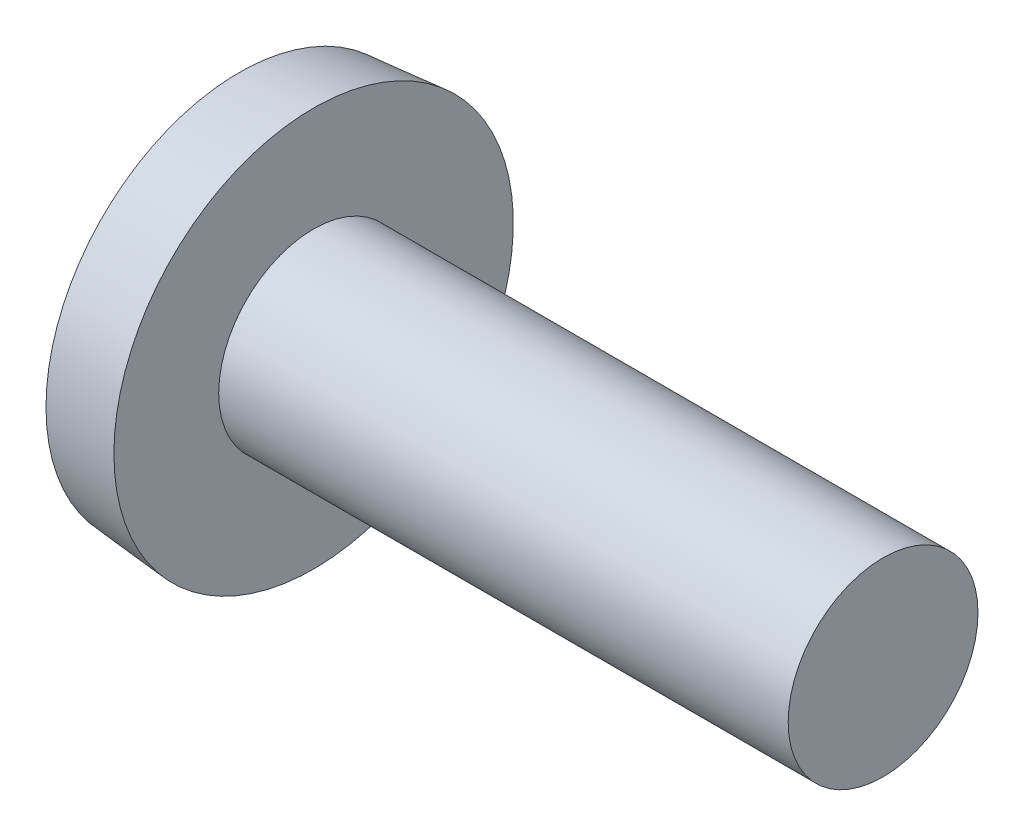
SolidWorks part; units mm, degrees
ref_plane "Plane1" through (0, 0, 0) normal (0, 0, 1) x (1, 0, 0)
ref_plane "Plane2" through (0, 0, 0) normal (0, 1, 0) x (1, 0, 0)
ref_plane "Plane3" through (0, 0, 0) normal (1, 0, 0) x (0, 0, -1)
sketch "BodySke" plane through (0, 0, 0) normal (0, 0, 1) x (1, 0, 0)
  line L0 (1.9812, 1.5875) -> (1.9812, 3.3401)
  line L1 (1.9812, 3.3401) -> (0.7366, 3.2312)
  line L2 (-25.4, 0) -> (127, 0) construction
  line L3 (1.9812, -3.3401) -> (0.7366, -3.2312) construction
  line L4 (1.9812, 1.5875) -> (11.5062, 1.5875)
  line L5 (11.5062, 1.5875) -> (11.5062, 0)
  line L6 (11.5062, 0) -> (0, 0)
  line L7 (1.9812, -1.5875) -> (11.5062, -1.5875) construction
  line L8 (2.6162, 6.35) -> (2.6162, -3.175) construction
  line L9 (1.9812, 6.35) -> (1.9812, -3.175) construction
  arc A0 (0, 0) -> (0.7366, 3.2312) centre (7.4554, 0) cw
  dimension "Head_ang" = 85
  dimension "Oval_ht" = 0.7366
  dimension "Head_ht" = 1.9812
  dimension "Diameter" = 3.175
  dimension "Length" = 9.525
  dimension "Head_dia" = 6.6802
  dimension "Advance" = 0.635
  dimension "Thread_nom" = 9.525
revolve "Base-Revolve" add sketch "BodySke" angle 360 about L2
cosmetic thread "ThreadCosmetic" [suppressed] parameters "Thread_length"=4.0691, "Thread_minor"=2.4181
sketch "Sketch2" plane through (0, 0, 0) normal (1, 0, 0) x (0, 0, -1)
  line L0 (3.3401, -0.5461) -> (3.3401, 0.5461)
  line L1 (3.3401, 0.5461) -> (-3.3401, 0.5461)
  line L2 (-3.3401, 0.5461) -> (-3.3401, -0.5461)
  line L3 (-3.3401, -0.5461) -> (3.3401, -0.5461)
  dimension "D1" = 8.7376
  dimension "D2" = 4.3688
  dimension "D3" = 0.6858
  dimension "Slot_width" = 1.0922
extrude "Slot" [suppressed] cut sketch "Sketch2" along normal blind 1.2192
sketch "Sketch3" plane through (0, 0, 0) normal (1, 0, 0) x (0, 0, -1)
  line L0 (-0.4572, 2.1844) -> (0.4572, 2.1844)
  line L1 (0.4572, 2.1844) -> (0.4572, -2.1844)
  line L2 (0.4572, -2.1844) -> (-0.4572, -2.1844)
  line L3 (-0.4572, -2.1844) -> (-0.4572, 2.1844)
  dimension "D1" = 0.5588
  dimension "Cross_width" = 0.9144
  dimension "D2" = 2.8448
  dimension "Cross_dia" = 4.3688
ref_plane "Plane4" through (2.4892, 0, 0) normal (1, 0, 0) x (0, 0, -1)
sketch "Sketch4" plane through (2.4892, 0, 0) normal (1, 0, 0) x (0, 0, -1)
  line L0 (-0.2286, 0.2286) -> (0.2286, 0.2286)
  line L1 (0.2286, 0.2286) -> (0.2286, -0.2286)
  line L2 (0.2286, -0.2286) -> (-0.2286, -0.2286)
  line L3 (-0.2286, -0.2286) -> (-0.2286, 0.2286)
  dimension "D1" = 0.5588
  dimension "D2" = 0.2794
  dimension "D3" = 0.5588
  dimension "D4" = 0.2794
loft "Cross" cut profiles "Sketch3", "Sketch4"
pattern_circular "CirPattern1" count 2 every 90 about axis through (0, 0, 0) along (1, 0, 0) of "Cross"
sketch "ThdSchSke" plane through (0, 0, 0) normal (0, 0, 1) x (1, 0, 0)
  line L0 (2.6162, -1.209) -> (2.3512, -1.5875)
  line L1 (2.6162, -1.209) -> (2.8812, -1.5875)
  line L2 (2.8812, -1.5875) -> (2.8812, -1.9844)
  line L3 (-3.175, 0) -> (5.1513, 0) construction
  line L5 (2.8812, -1.9844) -> (2.3512, -1.9844)
  line L6 (2.3512, -1.9844) -> (2.3512, -1.5875)
  dimension "Thread_minor" = 3.3249
  dimension "Diameter" = 4.1656
  dimension "Start" = 3.3731
  dimension "SideAngle" = 55
  dimension "VeeAngle" = 70
  dimension "Overcut" = 5.207
revolve "ThreadSchematic" [suppressed] cut sketch "ThdSchSke" angle 360 about L3
pattern_linear "ThdSchPat" [suppressed]
equation "\"D1@Sketch3\" = \"Cross_width@Sketch3\" / 2"
equation "\"D2@Sketch3\" = \"Cross_dia@Sketch3\" / 2"
equation "\"D1@Sketch4\" = \"Cross_width@Sketch3\"*.5"
equation "\"D2@Sketch4\" = \"D1@Sketch4\" / 2"
equation "\"D3@Sketch4\" = \"D1@Sketch4\""
equation "\"D4@Sketch4\" = \"D2@Sketch4\""
equation "\"D1@Sketch2\" = \"Head_dia@BodySke\""
equation "\"D2@Sketch2\" = \"D1@Sketch2\" / 2"
equation "\"D3@Sketch2\" = \"Slot_width@Sketch2\" / 2"
equation "\"Thread_length@ThreadCosmetic\" = ((sgn( (\"Length@BodySke\" - \"Advance@BodySke\" ) - \"Thread_nom@BodySke\" )-1)*( (\"Length@BodySke\" - \"Advance@BodySke\" ) - \"Thread_nom@BodySke\" ))/-2+ \"Thread_nom@BodySke\""
equation "\"Thread_minor@ThdSchSke\" = \"Thread_minor@ThreadCosmetic\""
equation "\"Diameter@ThdSchSke\" = \"Diameter@BodySke\""
equation "\"Overcut@ThdSchSke\" = \"Diameter@BodySke\" * 1.25"
equation "\"Start@ThdSchSke\" = \"Head_ht@BodySke\" + \"Length@BodySke\" - \"Thread_length@ThreadCosmetic\"  '---Non-countersunk---"
equation "\"Num_threads@ThdSchPat\" = int( \"Thread_length@ThreadCosmetic\" / \"Advance@BodySke\" + 0.999 )  + 1"
equation "\"Advance@ThdSchPat\" = \"Thread_length@ThreadCosmetic\" /  (\"Num_threads@ThdSchPat\" - 1) 'relax it"
